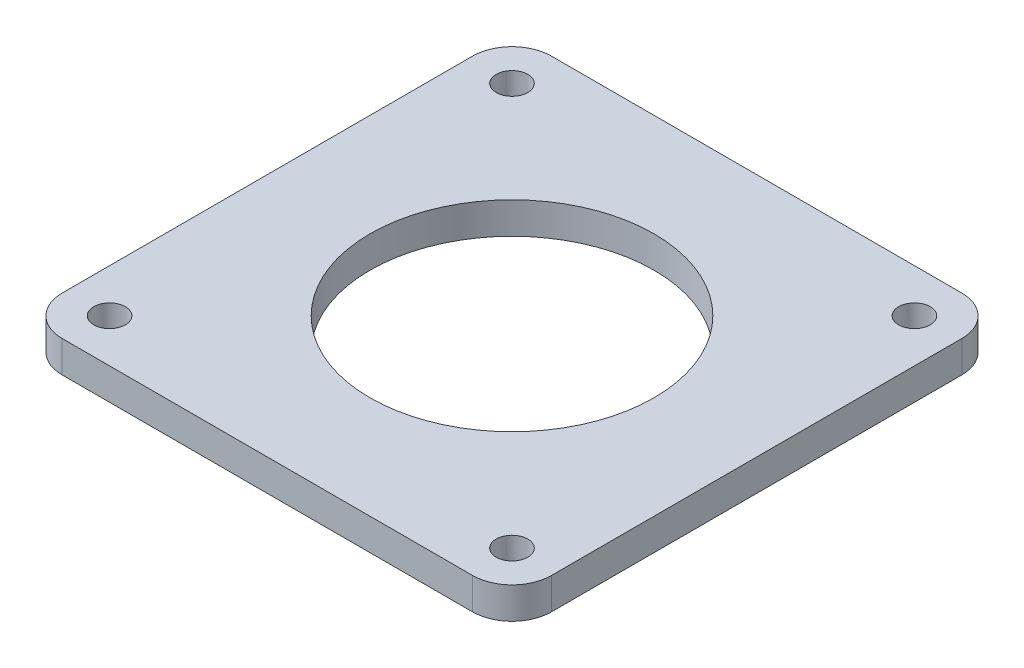
SolidWorks part; units mm, degrees
ref_plane "Front Plane" through (0, 0, 0) normal (0, 0, 1) x (1, 0, 0)
ref_plane "Top Plane" through (0, 0, 0) normal (0, 1, 0) x (1, 0, 0)
ref_plane "Right Plane" through (0, 0, 0) normal (1, 0, 0) x (0, 0, -1)
sketch "Sketch1" plane through (0, 0, 0) normal (0, 1, 0) x (1, 0, 0)
  line L0 (0, 0) -> (0, 31) construction
  line L1 (-31, -31) -> (31, -31)
  line L2 (-31, -31) -> (-31, 31)
  line L3 (-31, 31) -> (31, 31)
  line L4 (31, -31) -> (31, 31)
  line L5 (-31, -31) -> (31, 31) construction
  line L6 (-31, 31) -> (31, -31) construction
  line L7 (-31, 31) -> (-25.5, 31)
  line L8 (-31, 31) -> (-31, 25.5)
  line L9 (-31, 25.5) -> (-25.5, 25.5) construction
  line L10 (-25.5, 31) -> (-25.5, 25.5) construction
  line L11 (-31, 31) -> (-25.5, 25.5) construction
  line L12 (-31, 25.5) -> (-25.5, 31) construction
  line L13 (0, 0) -> (31, 0) construction
  circle A0 centre (-25.5, 25.5) radius 2
  circle A1 centre (25.5, 25.5) radius 2
  circle A2 centre (25.5, -25.5) radius 2
  circle A3 centre (-25.5, -25.5) radius 2
  point P0 (0, 0)
  point P9 (-28.25, 28.25)
  dimension "D5" = 4
  dimension "D1" = 62
  dimension "D2" = 62
  dimension "D3" = 5.5
  dimension "D4" = 5.5
extrude "Boss-Extrude1" add sketch "Sketch1" along normal blind 4 contours L1 L4 L3 L2 A1 A0 A2 A3
sketch "Sketch2" plane through (0, 4, 0) normal (0, 1, 0) x (1, 0, 0)
  circle A0 centre (0, 0) radius 18
  dimension "D1" = 36
extrude "Cut-Extrude1" cut sketch "Sketch2" against normal blind 10
fillet "Fillet1" radius 5 4 edges at (-31, 2, 31) (31, 2, -31) (-31, 2, -31) (31, 2, 31)
